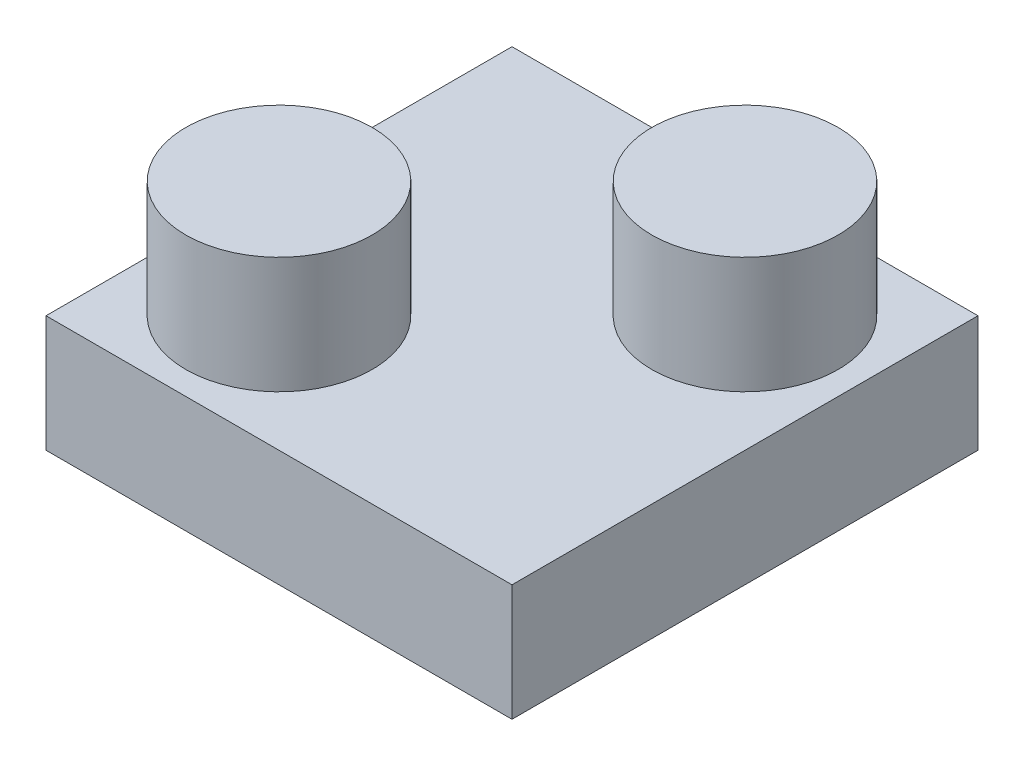
SolidWorks part; units mm, degrees
ref_plane "Front Plane" through (0, 0, 0) normal (0, 0, 1) x (1, 0, 0)
ref_plane "Top Plane" through (0, 0, 0) normal (0, 1, 0) x (1, 0, 0)
ref_plane "Right Plane" through (0, 0, 0) normal (1, 0, 0) x (0, 0, -1)
sketch "Sketch1" plane through (0, 0, 0) normal (0, 1, 0) x (1, 0, 0)
  line L1 (5, -5) -> (-5, -5)
  line L2 (5, -5) -> (5, 5)
  line L3 (5, 5) -> (-5, 5)
  line L4 (-5, -5) -> (-5, 5)
  line L5 (5, -5) -> (-5, 5) construction
  line L6 (5, 5) -> (-5, -5) construction
  point P0 (0, 0)
  dimension "D1" = 10
  dimension "D2" = 10
extrude "Boss-Extrude1" add sketch "Sketch1" along normal blind 5
sketch "Sketch2" plane through (0, 5, 0) normal (0, 1, 0) x (1, 0, 0)
  line L0 (5, 5) -> (-5, -5) construction
  line L1 (5, -5) -> (5, 5) construction
  line L3 (-5, 5) -> (-5, -5) construction
  line L6 (5, -5) -> (-5, -5)
  line L7 (5, -5) -> (5, 5)
  line L8 (5, 5) -> (-5, 5)
  line L9 (-5, -5) -> (-5, 5)
  circle A0 centre (-2.5, -2.5) radius 2
  circle A1 centre (2.5, 2.5) radius 2
  dimension "D1" = 4
  dimension "D2" = 4
  dimension "D3" = 2.5
  dimension "D4" = 2.5
extrude "Cut-Extrude1" cut sketch "Sketch2" against normal blind 2.5
